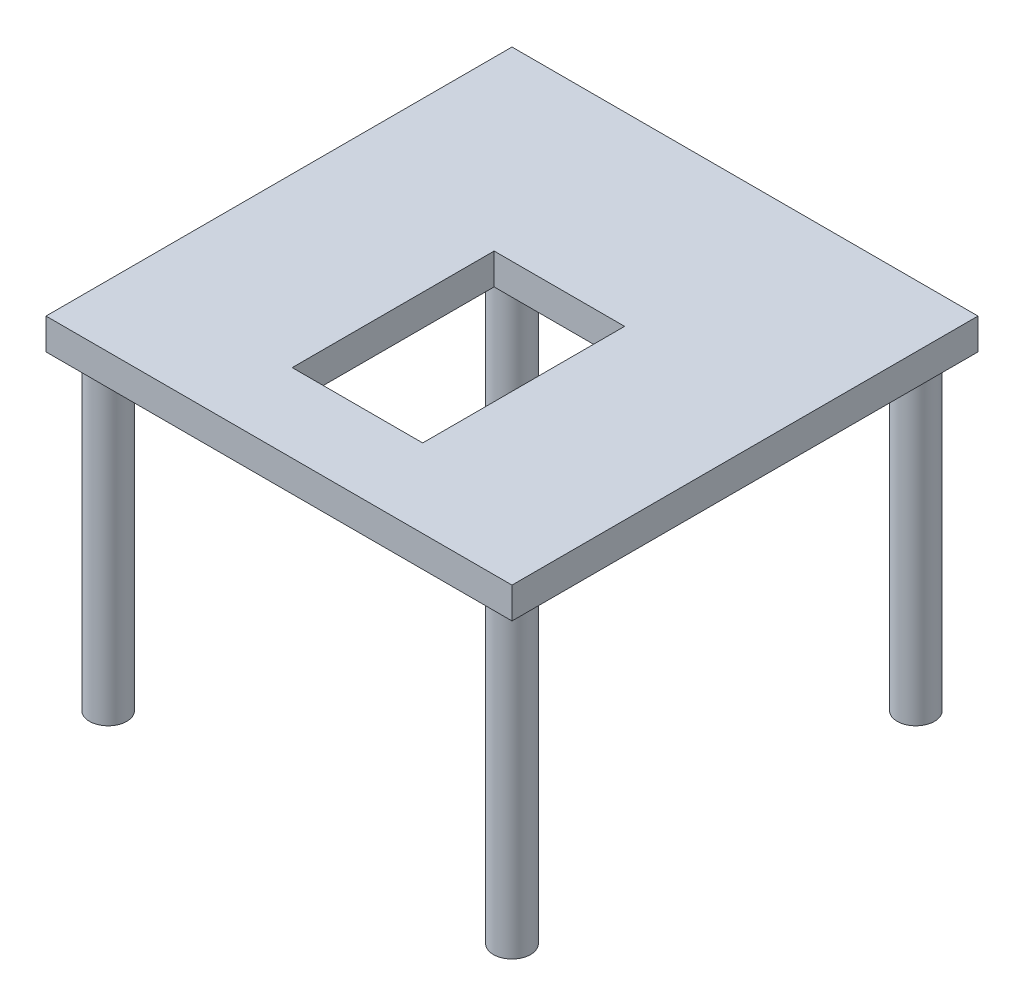
SolidWorks part; units mm, degrees
material "1060 Alloy"
ref_plane "Front Plane" through (0, 0, 0) normal (0, 0, 1) x (1, 0, 0)
ref_plane "Top Plane" through (0, 0, 0) normal (0, 1, 0) x (1, 0, 0)
ref_plane "Right Plane" through (0, 0, 0) normal (1, 0, 0) x (0, 0, -1)
sketch "Sketch1" plane through (0, 0, 0) normal (0, 1, 0) x (1, 0, 0)
  line L1 (-75, -75) -> (75, -75)
  line L2 (-75, -75) -> (-75, 75)
  line L3 (-75, 75) -> (75, 75)
  line L4 (75, -75) -> (75, 75)
  line L5 (-75, -75) -> (75, 75) construction
  line L6 (-75, 75) -> (75, -75) construction
  point P0 (0, 0)
  dimension "D1" = 150
  dimension "D2" = 150
extrude "Boss-Extrude2" add sketch "Sketch1" along normal blind 10
sketch "Sketch3" plane through (0, 0, 0) normal (0, -1, 0) x (1, 0, 0)
  line L14 (-65, -65) -> (65, -65)
  line L15 (65, -65) -> (65, 65)
  line L16 (65, 65) -> (-65, 65)
  line L17 (-65, 65) -> (-65, -65)
  line L18 (-65, -65) -> (65, -65)
  line L19 (65, -65) -> (65, 65)
  line L20 (65, 65) -> (-65, 65)
  line L21 (-65, 65) -> (-65, -65)
  circle A0 centre (-65, 65) radius 6
  circle A1 centre (65, 65) radius 6
  circle A2 centre (65, -65) radius 6
  circle A3 centre (-65, -65) radius 6
  dimension "D2" = 12
  dimension "D3" = 12
  dimension "D4" = 12
  dimension "D5" = 12
  dimension "D1" = 10
extrude "Boss-Extrude3" add sketch "Sketch3" along normal blind 100 contours L20 A0 L21 | L19 A1 L20 | L20 A1 L19 | L21 A0 L20 | L18 A3 L21 | L21 A3 L18 | L18 A2 L19 | L19 A2 L18
sketch "Sketch4" plane through (0, 10, 0) normal (0, 1, 0) x (1, 0, 0)
  line L0 (0, 0) -> (0, -17.25)
  line L2 (-21, -49.75) -> (21, -49.75)
  line L3 (-21, -49.75) -> (-21, 15.25)
  line L4 (-21, 15.25) -> (21, 15.25)
  line L5 (21, -49.75) -> (21, 15.25)
  line L6 (-21, -49.75) -> (21, 15.25) construction
  line L7 (-21, 15.25) -> (21, -49.75) construction
  dimension "D1" = 65
  dimension "D2" = 42
  dimension "D3" = 17.25
extrude "Cut-Extrude1" cut sketch "Sketch4" against normal through all
